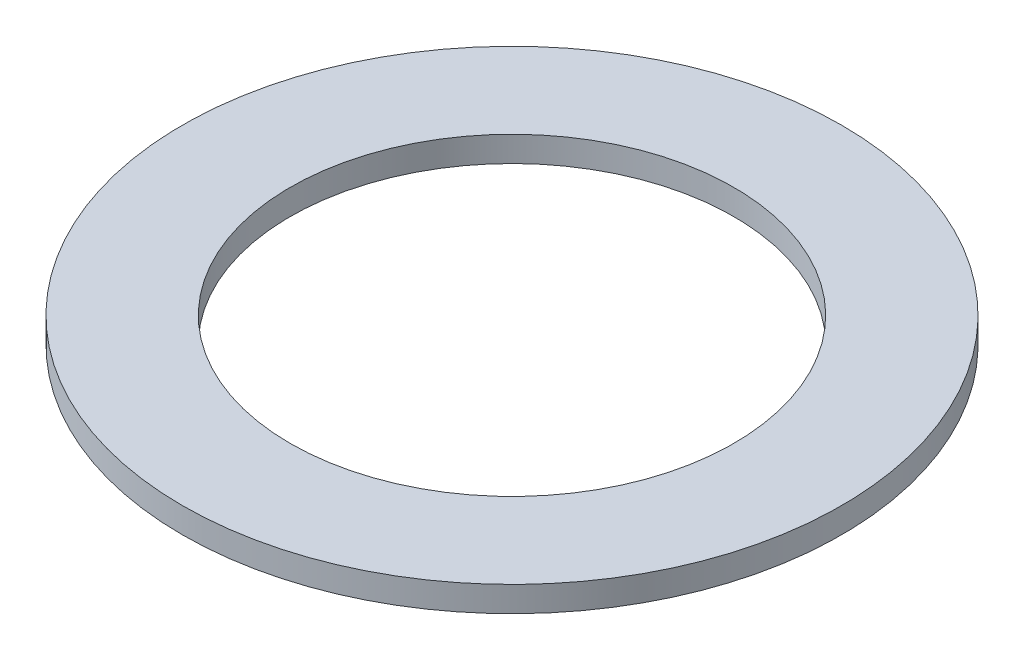
SolidWorks part; units mm, degrees
ref_plane "Front Plane" through (0, 0, 0) normal (0, 0, 1) x (1, 0, 0)
ref_plane "Top Plane" through (0, 0, 0) normal (0, 1, 0) x (1, 0, 0)
ref_plane "Right Plane" through (0, 0, 0) normal (1, 0, 0) x (0, 0, -1)
sketch "Sketch1" plane through (0, 0, 0) normal (0, 1, 0) x (1, 0, 0)
  circle A0 centre (0, 0) radius 26
  circle A1 centre (0, 0) radius 17.5
  dimension "D1" = 52
  dimension "D2" = 35
extrude "Boss-Extrude1" add sketch "Sketch1" along normal blind 2
